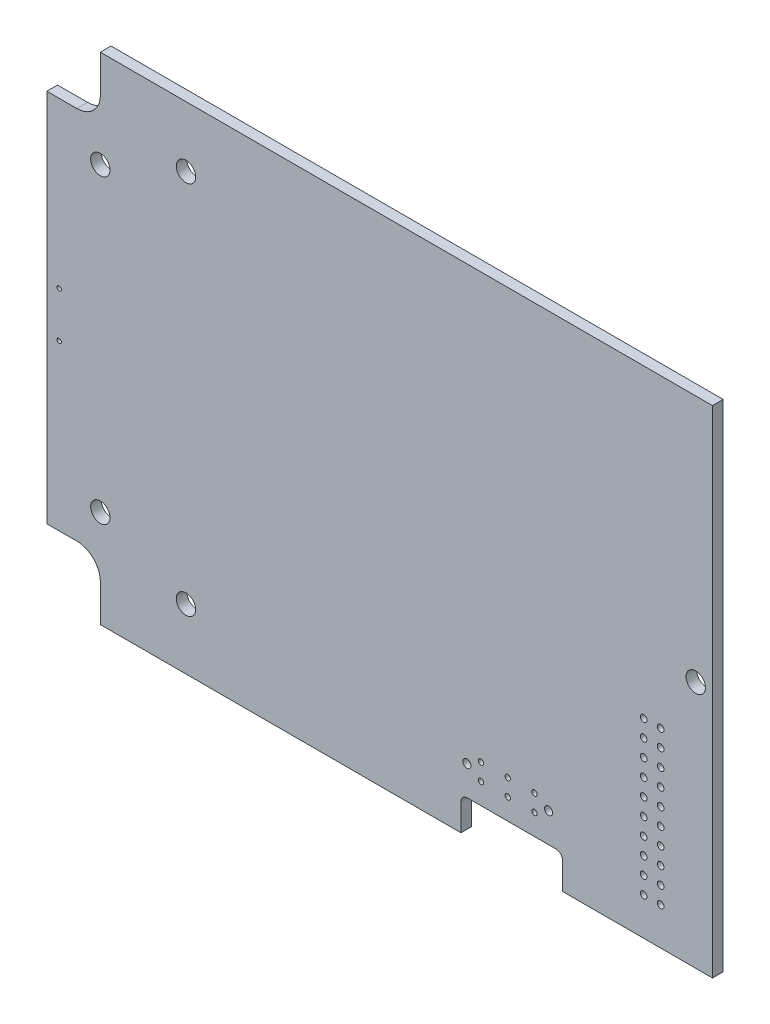
SolidWorks part; units mm, degrees
ref_plane "Płaszczyzna przednia" through (0, 0, 0) normal (0, 0, 1) x (1, 0, 0)
ref_plane "Płaszczyzna górna" through (0, 0, 0) normal (0, 1, 0) x (1, 0, 0)
ref_plane "Płaszczyzna prawa" through (0, 0, 0) normal (1, 0, 0) x (0, 0, -1)
sketch "Sketch1" plane through (0, 0, 0) normal (0, 0, 1) x (1, 0, 0)
  line L7 (246.9504, 63.2305) -> (246.9504, 62.5305) construction
  line L8 (246.9504, 62.5305) -> (245.4504, 62.5305) construction
  line L9 (245.4504, -11.1695) -> (246.9504, -11.1695) construction
  line L10 (246.9504, -11.1695) -> (246.9504, -11.8695) construction
  line L11 (246.9504, -11.8695) -> (393.5004, -11.8695) construction
  line L12 (393.5004, 63.2305) -> (246.9504, 63.2305) construction
  line L13 (245.4504, 62.5305) -> (245.4504, -11.1695) construction
  line L15 (393.5004, -11.8695) -> (393.5004, 63.2305) construction
  line L16 (393.5004, 63.2305) -> (393.5004, 1065.7805) construction
  line L17 (393.5004, -1014.4195) -> (393.5004, -11.8695) construction
  circle A9 centre (347.2504, -2.3195) radius 3 construction
  circle A10 centre (342.9504, 25.6805) radius 2.5 construction
  circle A11 centre (347.2504, 53.6805) radius 3 construction
  circle A12 centre (266.7504, 53.6805) radius 3 construction
  circle A13 centre (253.9504, 48.1805) radius 2.5 construction
  circle A14 centre (266.7504, -2.3195) radius 3 construction
  circle A15 centre (253.9504, 3.1805) radius 2.5 construction
  circle A16 centre (250.4504, -5.8195) radius 3 construction
  circle A17 centre (250.4504, 57.1805) radius 3 construction
  circle A31 centre (375.4504, -5.8195) radius 3 construction
  circle A32 centre (375.4504, -5.8195) radius 1.6 construction
  circle A33 centre (375.4504, 57.1805) radius 3 construction
  circle A34 centre (375.4504, 57.1805) radius 1.6 construction
  circle A35 centre (347.2504, 53.6805) radius 1 construction
  circle A36 centre (342.9504, 25.6805) radius 1 construction
  circle A37 centre (347.2504, -2.3195) radius 1 construction
  circle A38 centre (266.7504, -2.3195) radius 1 construction
  circle A39 centre (253.9504, 3.1805) radius 1 construction
  circle A40 centre (250.4504, -5.8195) radius 1.6 construction
  circle A41 centre (253.9504, 48.1805) radius 1 construction
  circle A42 centre (266.7504, 53.6805) radius 1 construction
  circle A43 centre (250.4504, 57.1805) radius 1.6 construction
sketch "Sketch2" plane through (0, 0, 0) normal (0, 0, 1) x (1, 0, 0)
  line L0 (378.4504, 63.2305) -> (372.4504, 63.2305) construction
  line L1 (372.4504, 63.2305) -> (253.4504, 63.2305) construction
  line L2 (372.4504, -11.8695) -> (378.4504, -11.8695) construction
  line L3 (378.4504, -11.8695) -> (393.5004, -11.8695) construction
  line L4 (246.9504, -11.8695) -> (253.4504, -11.8695) construction
  line L5 (245.4504, -2.8195) -> (245.4504, -11.1695) construction
  line L6 (253.4504, 63.2305) -> (246.9504, 63.2305) construction
  line L7 (245.4504, 62.5305) -> (245.4504, 54.1805) construction
  line L16 (393.5004, 63.2305) -> (246.9504, 63.2305) construction
  line L17 (246.9504, 63.2305) -> (246.9504, 62.5305) construction
  line L18 (246.9504, 62.5305) -> (245.4504, 62.5305) construction
  line L19 (245.4504, 62.5305) -> (245.4504, -11.1695) construction
  line L20 (245.4504, -11.1695) -> (246.9504, -11.1695) construction
  line L21 (246.9504, -11.1695) -> (246.9504, -11.8695) construction
  line L22 (246.9504, -11.8695) -> (393.5004, -11.8695) construction
  line L23 (393.5004, -11.8695) -> (393.5004, 63.2305) construction
  line L24 (393.5004, 63.2305) -> (378.4504, 63.2305) construction
  line L25 (246.9504, 63.2305) -> (246.9504, 62.5305) construction
  line L26 (246.9504, 62.5305) -> (245.4504, 62.5305) construction
  line L27 (245.4504, 54.1805) -> (245.4504, -2.8195) construction
  line L28 (245.4504, -11.1695) -> (246.9504, -11.1695) construction
  line L29 (246.9504, -11.1695) -> (246.9504, -11.8695) construction
  line L30 (253.4504, -11.8695) -> (372.4504, -11.8695) construction
  line L31 (393.5004, -11.8695) -> (393.5004, 63.2305) construction
  line L32 (253.4504, 63.2305) -> (253.4504, 57.1805) construction
  line L33 (250.4504, 54.1805) -> (245.4504, 54.1805) construction
  line L34 (250.4504, -2.8195) -> (245.4504, -2.8195) construction
  line L35 (253.4504, -5.8195) -> (253.4504, -11.8695) construction
  line L36 (372.4504, -5.8195) -> (372.4504, -11.8695) construction
  line L37 (378.4504, -5.8195) -> (378.4504, -11.8695) construction
  line L38 (378.4504, 57.1805) -> (378.4504, 63.2305) construction
  line L39 (372.4504, 57.1805) -> (372.4504, 63.2305) construction
  line L40 (371.9504, 62.7305) -> (253.9504, 62.7305)
  line L41 (253.9504, 62.7305) -> (253.9504, 57.1805)
  line L42 (250.4504, 53.6805) -> (245.9504, 53.6805)
  line L43 (245.9504, 53.6805) -> (245.9504, -2.3195)
  line L44 (250.4504, -2.3195) -> (245.9504, -2.3195)
  line L45 (253.9504, -5.8195) -> (253.9504, -11.3695)
  line L46 (253.9504, -11.3695) -> (371.9504, -11.3695)
  line L47 (371.9504, -5.8195) -> (371.9504, -11.3695)
  line L48 (378.9504, -5.8195) -> (378.9504, -11.3695)
  line L49 (378.9504, -11.3695) -> (393.0004, -11.3695)
  line L50 (393.0004, -11.3695) -> (393.0004, 62.7305)
  line L51 (393.0004, 62.7305) -> (378.9504, 62.7305)
  line L52 (378.9504, 57.1805) -> (378.9504, 62.7305)
  line L53 (371.9504, 57.1805) -> (371.9504, 62.7305)
  circle A0 centre (250.4504, -5.8195) radius 3 construction
  circle A1 centre (375.4504, -5.8195) radius 3 construction
  circle A2 centre (375.4504, 57.1805) radius 3 construction
  circle A3 centre (250.4504, 57.1805) radius 3 construction
  arc A4 (253.4504, -5.8195) -> (250.4504, -2.8195) centre (250.4504, -5.8195) ccw construction
  arc A5 (378.4504, -5.8195) -> (372.4504, -5.8195) centre (375.4504, -5.8195) ccw construction
  arc A6 (372.4504, 57.1805) -> (378.4504, 57.1805) centre (375.4504, 57.1805) ccw construction
  arc A7 (250.4504, 54.1805) -> (253.4504, 57.1805) centre (250.4504, 57.1805) ccw construction
  arc A8 (378.4504, 57.1805) -> (372.4504, 57.1805) centre (375.4504, 57.1805) ccw construction
  arc A9 (372.4504, -5.8195) -> (378.4504, -5.8195) centre (375.4504, -5.8195) ccw construction
  arc A10 (250.4504, -2.8195) -> (253.4504, -5.8195) centre (250.4504, -5.8195) ccw construction
  arc A11 (253.4504, 57.1805) -> (250.4504, 54.1805) centre (250.4504, 57.1805) ccw construction
  arc A12 (250.4504, 53.6805) -> (253.9504, 57.1805) centre (250.4504, 57.1805) ccw
  arc A13 (253.9504, -5.8195) -> (250.4504, -2.3195) centre (250.4504, -5.8195) ccw
  arc A14 (378.9504, -5.8195) -> (371.9504, -5.8195) centre (375.4504, -5.8195) ccw
  arc A15 (371.9504, 57.1805) -> (378.9504, 57.1805) centre (375.4504, 57.1805) ccw
  point P2 (393.5004, 62.7305)
  point P4 (247.4504, 62.7305)
  point P18 (393.0004, -11.8695)
  point P19 (393.0004, 63.2305)
  dimension "D1" = 0.5
extrude "Boss-Extrude1" add sketch "Sketch2" along normal blind 1.6
hole_wizard "M2.5 Clearance Hole1" positions "Sketch3" profile "Sketch4" hole size "M2.5" standard "ISO" end condition through all
sketch "Sketch3" plane through (0, 0, 1.6) normal (0, 0, 1) x (1, 0, 0)
  point P1 (347.2504, -2.3195)
  point P3 (342.9504, 25.6805)
  point P5 (347.2504, 53.6805)
  point P7 (266.7504, -2.3195)
  point P9 (253.9504, 3.1805)
  point P11 (266.7504, 53.6805)
  point P13 (253.9504, 48.1805)
sketch "Sketch4" plane through (347.2504, -2.3195, 1.6) normal (1, 0, 0) x (0, -1, 0)
  line L0 (0, 0) -> (0, 1.6)
  line L1 (0, 1.6) -> (1.45, 1.6)
  line L2 (1.45, 1.6) -> (1.45, 0)
  line L5 (1.45, 0) -> (0, 0)
  line L11 (0, -6.35) -> (0, 107.95) construction
  dimension "Thru Hole Dia." = 2.9
  dimension "Thru Hole Depth" = 1.6
sketch "Sketch5" plane through (0, 0, 1.6) normal (0, 0, 1) x (1, 0, 0)
  line L0 (371.9504, 62.7305) -> (253.9504, 62.7305) construction
  line L1 (393.0004, -11.3695) -> (345.4504, -11.3695)
  line L2 (393.0004, -11.3695) -> (393.0004, 62.7305)
  line L3 (393.0004, 62.7305) -> (345.4504, 62.7305)
  line L4 (345.4504, -11.3695) -> (345.4504, 62.7305)
  line L5 (245.4504, 62.5305) -> (245.4504, -11.1695) construction
  dimension "D1" = 100
extrude "Cut-Extrude1" cut sketch "Sketch5" against normal through all
sketch "Sketch6" plane through (0, 0, 0) normal (0, 0, -1) x (-1, 0, 0)
  circle A0 centre (-247.8005, 29.0805) radius 0.325 construction
  circle A1 centre (-247.8005, 22.2805) radius 0.325 construction
  circle A2 centre (-247.8005, 29.0805) radius 0.325
  circle A3 centre (-247.8005, 22.2805) radius 0.325
extrude "Cut-Extrude2" cut sketch "Sketch6" against normal through all
sketch "Sketch7" plane through (0, 0, 0) normal (0, 0, -1) x (-1, 0, 0)
  line L0 (-307.8504, -7.3695) -> (-307.8504, -12.3195) construction
  line L1 (-323.0504, -12.3195) -> (-323.0504, -7.3695) construction
  line L2 (-322.0504, -6.3695) -> (-308.8504, -6.3695) construction
  line L3 (-307.8504, -7.3695) -> (-307.8504, -12.3195)
  line L4 (-323.0504, -12.3195) -> (-323.0504, -7.3695)
  line L5 (-322.0504, -6.3695) -> (-308.8504, -6.3695)
  line L6 (-307.8504, -12.3195) -> (-323.0504, -12.3195)
  arc A0 (-322.0504, -6.3695) -> (-323.0504, -7.3695) centre (-322.0504, -7.3695) ccw construction
  arc A1 (-307.8504, -7.3695) -> (-308.8504, -6.3695) centre (-308.8504, -7.3695) ccw construction
  arc A2 (-322.0504, -6.3695) -> (-323.0504, -7.3695) centre (-322.0504, -7.3695) ccw
  arc A3 (-307.8504, -7.3695) -> (-308.8504, -6.3695) centre (-308.8504, -7.3695) ccw
extrude "Cut-Extrude3" cut sketch "Sketch7" against normal through all
sketch "Sketch9" plane through (0, 0, 0) normal (0, 0, -1) x (-1, 0, 0)
  circle A0 centre (-308.7504, -1.9695) radius 0.6 construction
  circle A1 centre (-310.8504, -3.2195) radius 0.4 construction
  circle A2 centre (-314.8504, -3.2195) radius 0.4 construction
  circle A3 centre (-314.8504, -0.7195) radius 0.4 construction
  circle A4 centre (-318.8504, -0.7195) radius 0.4 construction
  circle A5 centre (-318.8504, -3.2195) radius 0.4 construction
  circle A6 centre (-320.9504, -1.9695) radius 0.6 construction
  circle A7 centre (-308.7504, -1.9695) radius 0.6
  circle A8 centre (-310.8504, -3.2195) radius 0.4
  circle A9 centre (-314.8504, -3.2195) radius 0.4
  circle A10 centre (-314.8504, -0.7195) radius 0.4
  circle A11 centre (-318.8504, -0.7195) radius 0.4
  circle A12 centre (-318.8504, -3.2195) radius 0.4
  circle A13 centre (-320.9504, -1.9695) radius 0.6
  circle A14 centre (-310.8504, -0.7195) radius 0.4 construction
  circle A15 centre (-310.8504, -0.7195) radius 0.4
extrude "Cut-Extrude4" cut sketch "Sketch9" against normal through all
sketch "Sketch10" plane through (0, 0, 1.6) normal (0, 0, 1) x (1, 0, 0)
  circle A1 centre (335.1638, -5.7595) radius 0.5
  circle A2 centre (337.7038, -5.7595) radius 0.5
  circle A11 centre (337.7038, -3.2195) radius 0.5
  circle A20 centre (335.1638, -3.2195) radius 0.5
  circle A21 centre (335.1638, -0.6795) radius 0.5
  circle A22 centre (337.7038, -0.6795) radius 0.5
  circle A31 centre (335.1638, 1.8605) radius 0.5
  circle A32 centre (337.7038, 1.8605) radius 0.5
  circle A41 centre (335.1638, 4.4005) radius 0.5
  circle A42 centre (337.7038, 4.4005) radius 0.5
  circle A51 centre (335.1638, 6.9405) radius 0.5
  circle A52 centre (337.7038, 6.9405) radius 0.5
  circle A61 centre (335.1638, 9.4805) radius 0.5
  circle A62 centre (337.7038, 9.4805) radius 0.5
  circle A71 centre (335.1638, 12.0205) radius 0.5
  circle A72 centre (337.7038, 12.0205) radius 0.5
  circle A81 centre (335.1638, 14.5605) radius 0.5
  circle A82 centre (337.7038, 14.5605) radius 0.5
  circle A91 centre (335.1638, 17.1005) radius 0.5
  circle A92 centre (337.7038, 17.1005) radius 0.5
  circle A101 centre (318.8504, -3.2195) radius 0.4 construction
  circle A102 centre (318.8504, -3.2195) radius 0.4 construction
  circle A103 centre (342.9504, -4.3195) radius 1.75 construction
  circle A104 centre (342.9504, -4.3195) radius 1.75 construction
  circle A105 centre (342.9504, -4.3195) radius 3 construction
  point P7 (335.2751, -6.1945)
  point P11 (0, 0)
  point P16 (0, 0)
  point P18 (335.2484, -4.7814)
  dimension "D1" = 1
  dimension "D5" = 6
  dimension "D4" = 16.51
  dimension "D6" = 2.54
  dimension "D7" = 2.54
  dimension "D8" = 2.54
  dimension "D2" = 2
  dimension "D3" = 10
extrude "Cut-Extrude5" cut sketch "Sketch10" against normal through all
